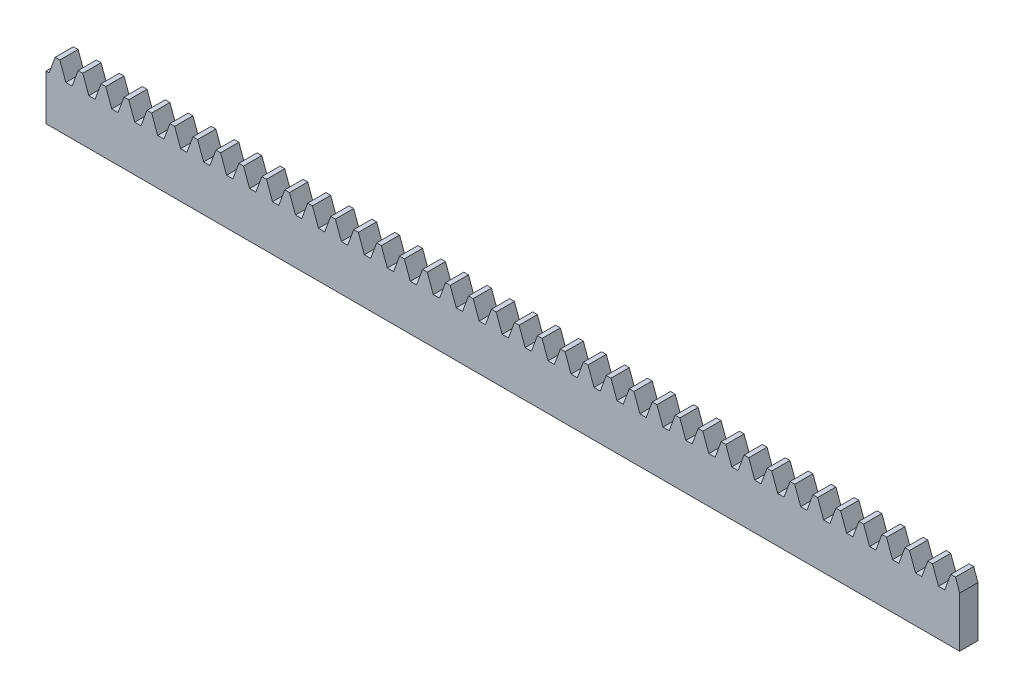
SolidWorks part; units mm, degrees
ref_plane "Plane1" through (0, 0, 0) normal (0, 0, 1) x (1, 0, 0)
ref_plane "Plane2" through (0, 0, 0) normal (0, 1, 0) x (1, 0, 0)
ref_plane "Plane3" through (0, 0, 0) normal (1, 0, 0) x (0, 0, -1)
sketch "HoldingSke" plane through (0, 0, 0) normal (0, 1, 0) x (1, 0, 0)
  line L0 (0, 0) -> (0.0696, 0.4951)
  line L1 (-15, 0) -> (100, 0) construction
  line L2 (0, 0) -> (-2.1039, 2.3779)
  line L3 (0, 0) -> (-11.863, 4.5341)
  line L4 (0, 0) -> (6.5177, 5.6657)
  line L5 (0, 0) -> (-23.7986, -8.8762)
  line L6 (0, 0) -> (-10.5278, -7.1032)
  line L9 (-71.009, 38.7566) -> (163.9142, 124.2616)
  line L10 (-76.2, 4.3779) -> (-61.2, 4.3779)
  line L11 (0, 0) -> (-5, 0)
  line L12 (-76.2, 101.6) -> (-76.133, 101.6)
  line L13 (24.9733, 27.94) -> (52.9518, 28.4284)
  line L14 (24.9733, 27.94) -> (24.9743, 27.94)
  line L15 (24.9733, 27.94) -> (100.4006, 29.5858)
  circle A0 centre (0, 0) radius 19.05
  circle A1 centre (0, 0) radius 7.5
  circle A2 centre (0, 0) radius 12.7
  dimension "MPH" = 15
  dimension "Diameter" = 38.1
  dimension "Num_teeth" = 41
  dimension "Pitch" = 0.5
  dimension "Width" = 5
  dimension "Show_teeth" = 998
  dimension "Thickness" = 12.7
  dimension "Ap" = 20
  dimension "Pitch_height" = 15
  dimension "Backlash" = 0.067
  dimension "Addendum_fac" = 1
  dimension "Dedendum_fac" = 1.25
  dimension "Clearance_fac" = 0.25
  dimension "Dedendum_add" = 0.001
  dimension "Length" = 250
  dimension "Module" = 2
sketch "BlankSke" plane through (0, 0, 0) normal (0, 0, 1) x (1, 0, 0)
  line L1 (0, 0) -> (250, 0)
  line L2 (0, 0) -> (0, 17)
  line L3 (0, 17) -> (250, 17)
  line L4 (250, 0) -> (250, 17)
  dimension "Length" = 250
  dimension "Blank_height" = 17
extrude "Blank" add sketch "BlankSke" against normal blind 5
sketch "TooCutSkeIll" plane through (0, 0, 0) normal (0, 0, 1) x (1, 0, 0)
  line L0 (-2.4806, 16.9474) -> (-0.9819, 12.8296)
  line L1 (-0.5111, 12.5) -> (0.5111, 12.5)
  line L2 (0.9819, 12.8296) -> (2.4806, 16.9474)
  line L3 (250, 17) -> (0, 17) construction
  line L4 (0, 0) -> (0, 64.897) construction
  line L5 (-13.208, 15) -> (12.954, 15) construction
  line L6 (0, 0) -> (250, 0) construction
  line L7 (1.7718, 15) -> (1.7718, 48.7463) construction
  line L8 (-1.7718, 15) -> (-1.7718, 48.7463) construction
  line L9 (2.5558, 17) -> (2.5558, 17.0254)
  line L10 (-2.5558, 17) -> (-2.5558, 17.0254)
  line L11 (-2.5558, 17.0254) -> (2.5558, 17.0254)
  arc A0 (0.5111, 12.5) -> (0.9819, 12.8296) centre (0.5111, 13.001) ccw
  arc A1 (-0.9819, 12.8296) -> (-0.5111, 12.5) centre (-0.5111, 13.001) ccw
  arc A2 (2.5558, 17) -> (2.4806, 16.9474) centre (2.5558, 16.92) ccw
  arc A3 (-2.4806, 16.9474) -> (-2.5558, 17) centre (-2.5558, 16.92) ccw
  dimension "Root_fillet" = 0.501
  dimension "Break_rad" = 0.08
  dimension "Pitch_height" = 15
  dimension "Gap_width" = 3.5436
  dimension "Dedendum" = 2.5
  dimension "Addendum_plus" = 2.0254
  dimension "Pressure_angle" = 20
extrude "ToothCutIll" [suppressed] cut sketch "TooCutSkeIll" against normal through all
sketch "TooCutSkeSim" plane through (0, 0, 0) normal (0, 0, 1) x (1, 0, 0)
  line L0 (0.8619, 12.5) -> (-0.8619, 12.5)
  line L1 (2.509, 17.0254) -> (0.8619, 12.5)
  line L2 (0, 17.4625) -> (0, 53.467) construction
  line L3 (2.509, 17.0254) -> (-2.509, 17.0254)
  line L6 (-2.509, 17.0254) -> (-0.8619, 12.5)
  line L9 (-1.7718, 15) -> (1.7718, 15) construction
  line L10 (0, 0) -> (250, 0) construction
  line L11 (1.7718, 15) -> (1.7718, 53.467) construction
  line L12 (-1.7718, 15) -> (-1.7718, 53.467) construction
  dimension "Pitch_height" = 15
  dimension "Pressure_angle" = 20
  dimension "Gap_width" = 3.5436
  dimension "Dedendum" = 2.5
  dimension "Addendum_plus" = 2.0254
extrude "ToothCutSim" cut sketch "TooCutSkeSim" against normal through all
pattern_linear "TeethCuts" count 40 spacing 6.2832 along (1, 0, 0) of "ToothCutIll", "ToothCutSim"
equation "' \"Module@HoldingSke\" = 6.35"
equation "' \"Num_teeth@HoldingSke\" = 12"
equation "' \"Ap@HoldingSke\" =  20"
equation "' \"Width@HoldingSke\" = 0.25 * 25.4"
equation "' \"Show_teeth@HoldingSke\" = 500"
equation "' \"Backlash@HoldingSke\" = 0.009 * 25.4"
equation "' \"Addendum_fac@HoldingSke\" = 1.0"
equation "' \"Dedendum_fac@HoldingSke\" = 1.25"
equation "' \"Dedendum_add@HoldingSke\" = 0.00005 * 25.4"
equation "' \"Clearance_fac@HoldingSke\" = 0.25"
equation "' \"Pitch_height@HoldingSke\" = 1 * 25.4"
equation "' \"Length@HoldingSke\" = 4.71 * 25.4"
equation "\"Pitch@HoldingSke\" = 1 / \"Module@HoldingSke\""
equation "\"MPH@HoldingSke\" = \"Dedendum_fac@HoldingSke\" / \"Pitch@HoldingSke\" + 2 * \"Dedendum_add@HoldingSke\" + 0.002 * 25.4"
equation "\"MPH@HoldingSke\" = ((sgn( \"MPH@HoldingSke\" - \"Pitch_height@HoldingSke\")+1)*( \"MPH@HoldingSke\" - \"Pitch_height@HoldingSke\"))/2 + \"Pitch_height@HoldingSke\""
equation "\"Blank_height@BlankSke\" = \"Pitch_height@HoldingSke\" + \"Addendum_fac@HoldingSke\"  / \"Pitch@HoldingSke\" "
equation "\"Length@BlankSke\" =  \"Length@HoldingSke\""
equation "\"Face_width@Blank\" = \"Width@HoldingSke\""
equation "\"Pressure_angle@TooCutSkeIll\" = \"Ap@HoldingSke\""
equation "\"Addendum_plus@TooCutSkeIll\" =  \"Addendum_fac@HoldingSke\"  / \"Pitch@HoldingSke\" + 0.001 *25.4"
equation "\"Dedendum@TooCutSkeIll\" = \"Dedendum_fac@HoldingSke\"  / \"Pitch@HoldingSke\""
equation "\"Pitch_height@TooCutSkeIll\" =  \"MPH@HoldingSke\""
equation "\"Gap_width@TooCutSkeIll\" = 3.14159265 / 2 / \"Pitch@HoldingSke\" + 6 * \"Backlash@HoldingSke\""
equation "\"Pressure_angle@TooCutSkeSim\" = \"Ap@HoldingSke\""
equation "\"Addendum_plus@TooCutSkeSim\" =  \"Addendum_fac@HoldingSke\"  / \"Pitch@HoldingSke\" + 0.001 * 25.4"
equation "\"Dedendum@TooCutSkeSim\" = \"Dedendum_fac@HoldingSke\"  / \"Pitch@HoldingSke\""
equation "\"Pitch_height@TooCutSkeSim\" =  \"MPH@HoldingSke\""
equation "\"Gap_width@TooCutSkeSim\" = 3.14159265 / 2 / \"Pitch@HoldingSke\" + 6 * \"Backlash@HoldingSke\""
equation "\"Root_fillet@TooCutSkeIll\" = \"Clearance_fac@HoldingSke\" / \"Pitch@HoldingSke\" + \"Dedendum_add@HoldingSke\""
equation "\"Break_rad@TooCutSkeIll\" = 0.02 / \"Pitch@HoldingSke\" * 2"
equation "\"Linear_pitch@TeethCuts\" = 3.14159265 / \"Pitch@HoldingSke\""
equation "\"Num_teeth@HoldingSke\" = int( ( \"Length@HoldingSke\" + 0 ) / (3.14159265 / \"Pitch@HoldingSke\")) + 0.9999  + 1"
equation " \"Num_teeth@TeethCuts\" = int( \"Show_teeth@HoldingSke\" ) + 1"
equation " \"Num_teeth@TeethCuts\" = ((sgn( \"Num_teeth@TeethCuts\" - \"Num_teeth@HoldingSke\" )-1)*( \"Num_teeth@TeethCuts\" - \"Num_teeth@HoldingSke\" ))/-2+ \"Num_teeth@HoldingSke\""
equation " \"Num_teeth@TeethCuts\" = ((sgn( \"Num_teeth@TeethCuts\" - 2.0)+1)*( \"Num_teeth@TeethCuts\" - 2.0))/2 +2.0"
